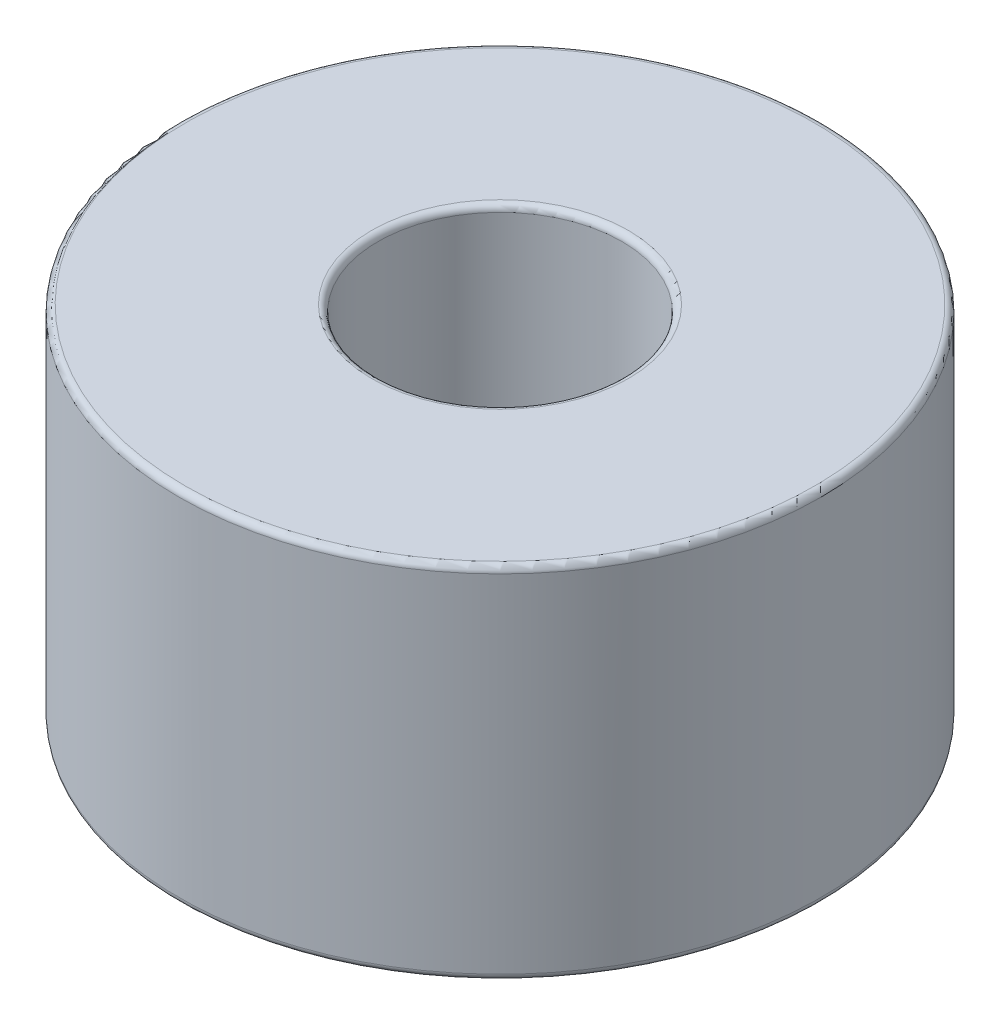
SolidWorks part; units mm, degrees
ref_plane "Front Plane" through (0, 0, 0) normal (0, 0, 1) x (1, 0, 0)
ref_plane "Top Plane" through (0, 0, 0) normal (0, 1, 0) x (1, 0, 0)
ref_plane "Right Plane" through (0, 0, 0) normal (1, 0, 0) x (0, 0, -1)
sketch "Sketch1" plane through (0, 0, 0) normal (0, 0, 1) x (1, 0, 0)
  line L0 (4.75, 0) -> (12.5, 0)
  line L1 (12.5, 0) -> (12.5, 14)
  line L2 (12.5, 14) -> (4.75, 14)
  line L3 (4.75, 14) -> (4.75, 0)
  line L4 (0, 0) -> (0, 14.7558) construction
  dimension "D1" = 12.5
  dimension "D2" = 4.75
  dimension "D3" = 14
revolve "Revolve1" add sketch "Sketch1" angle 360 about L4
fillet "Fillet1" radius 0.25 4 edges at (0, 0, -12.5) (0, 0, -4.75) (0, 14, -4.75) (0, 14, -12.5)
